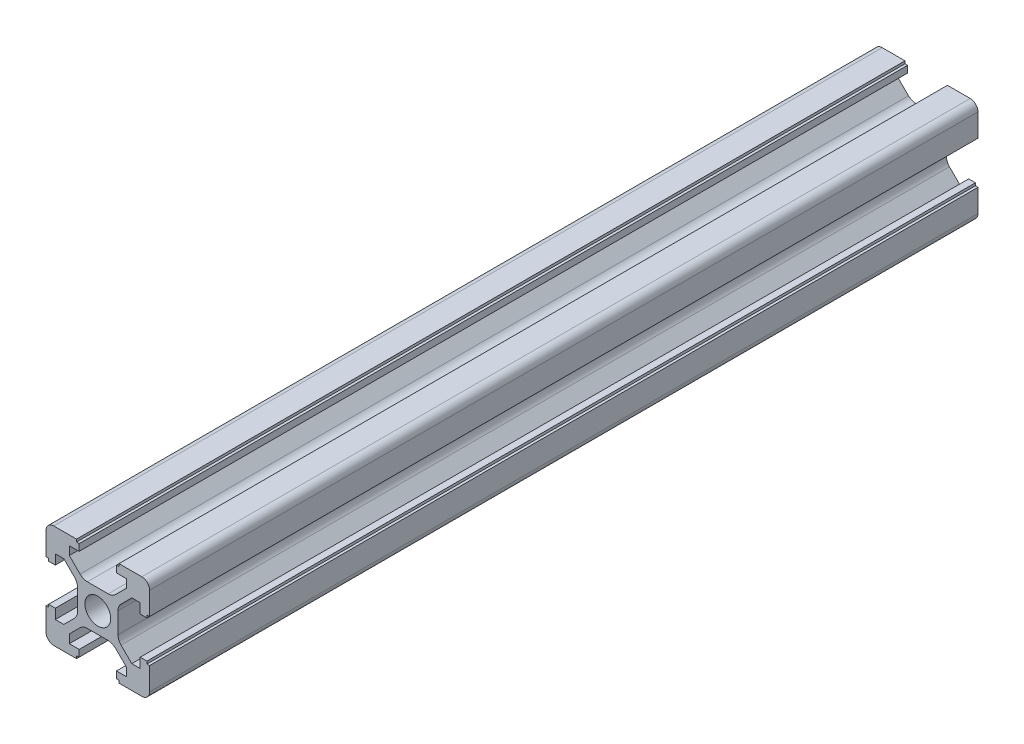
SolidWorks part; units mm, degrees
ref_plane "Front Plane" through (0, 0, 0) normal (0, 0, 1) x (1, 0, 0)
ref_plane "Top Plane" through (0, 0, 0) normal (0, 1, 0) x (1, 0, 0)
ref_plane "Right Plane" through (0, 0, 0) normal (1, 0, 0) x (0, 0, -1)
sketch "Sketch1" plane through (0, 0, 0) normal (0, 0, 1) x (1, 0, 0)
  line L0 (10, -4.1) -> (10, -8.5)
  line L1 (4.1, 10) -> (8.5, 10)
  line L2 (8.5, -10) -> (4.1, -10)
  line L3 (-8.5, -10) -> (-4.1, -10)
  line L4 (10, 8.5) -> (10, 4.1)
  line L7 (8.5, 10) -> (4.1, 10)
  line L8 (5.5, 6.5607) -> (3.4251, 4.4858)
  line L9 (8.5, 10) -> (4.1, 10)
  line L10 (3.9, 2.0109) -> (3.9, -2.0109)
  line L11 (2.0109, -3.9) -> (-2.0109, -3.9)
  line L12 (-3.9, -2.0109) -> (-3.9, 2.0109)
  line L13 (-2.0109, 3.9) -> (2.8393, 3.9)
  line L14 (2.5, 0) -> (22.2403, 0) construction
  line L15 (3.6, 9.5) -> (3.6, 8.2)
  line L16 (9.5, 3.6) -> (8.2, 3.6)
  line L17 (8.2, 3.6) -> (8.2, 5.5)
  line L18 (8.2, 5.5) -> (6.5607, 5.5)
  line L19 (10, -4.1) -> (10, -8.5)
  line L20 (4.1, 9.5) -> (3.6, 9.5)
  line L21 (4.1, 10) -> (4.1, 9.5)
  line L22 (8.5, 10) -> (4.1, 10)
  line L23 (10, 4.1) -> (9.5, 4.1)
  line L24 (9.5, 4.1) -> (9.5, 3.6)
  line L25 (5.5, 8.2) -> (5.5, 6.5607)
  line L26 (3.6, 8.2) -> (5.5, 8.2)
  line L27 (4.4858, 3.4251) -> (6.5607, 5.5)
  line L28 (10, -8.5) -> (10, -4.1)
  line L29 (6.5607, -5.5) -> (4.4858, -3.4251)
  line L30 (10, -8.5) -> (10, -4.1)
  line L31 (2.0109, -3.9) -> (-2.0109, -3.9)
  line L32 (3.9, 2.8393) -> (3.9, -2.0109)
  line L33 (9.5, -3.6) -> (8.2, -3.6)
  line L34 (3.6, -9.5) -> (3.6, -8.2)
  line L35 (3.6, -8.2) -> (5.5, -8.2)
  line L36 (5.5, -8.2) -> (5.5, -6.5607)
  line L37 (9.5, -4.1) -> (9.5, -3.6)
  line L38 (10, -4.1) -> (9.5, -4.1)
  line L39 (10, -8.5) -> (10, -4.1)
  line L40 (4.1, -10) -> (4.1, -9.5)
  line L41 (4.1, -9.5) -> (3.6, -9.5)
  line L42 (8.2, -5.5) -> (6.5607, -5.5)
  line L43 (8.2, -3.6) -> (8.2, -5.5)
  line L44 (3.4251, -4.4858) -> (5.5, -6.5607)
  line L45 (-4.1, -10) -> (-8.5, -10)
  line L46 (-10, -8.5) -> (-10, -4.1)
  line L47 (-8.5, -10) -> (-4.1, -10)
  line L48 (-5.5, -6.5607) -> (-3.4251, -4.4858)
  line L49 (-8.5, -10) -> (-4.1, -10)
  line L50 (-3.9, -2.0109) -> (-3.9, 2.0109)
  line L51 (2.0109, -3.9) -> (-2.0109, -3.9)
  line L52 (-3.6, -9.5) -> (-3.6, -8.2)
  line L53 (-9.5, -3.6) -> (-8.2, -3.6)
  line L54 (-8.2, -3.6) -> (-8.2, -5.5)
  line L55 (-8.2, -5.5) -> (-6.5607, -5.5)
  line L56 (-4.1, -9.5) -> (-3.6, -9.5)
  line L57 (-4.1, -10) -> (-4.1, -9.5)
  line L58 (-8.5, -10) -> (-4.1, -10)
  line L59 (-10, -4.1) -> (-9.5, -4.1)
  line L60 (-9.5, -4.1) -> (-9.5, -3.6)
  line L61 (-5.5, -8.2) -> (-5.5, -6.5607)
  line L62 (-3.6, -8.2) -> (-5.5, -8.2)
  line L63 (-4.4858, -3.4251) -> (-6.5607, -5.5)
  line L64 (-10, 4.1) -> (-10, 8.5)
  line L65 (-8.5, 10) -> (-4.1, 10)
  line L66 (-10, 8.5) -> (-10, 4.1)
  line L67 (-6.5607, 5.5) -> (-4.4858, 3.4251)
  line L68 (-10, 8.5) -> (-10, 4.1)
  line L69 (-2.0109, 3.9) -> (2.0109, 3.9)
  line L70 (-3.9, -2.0109) -> (-3.9, 2.0109)
  line L71 (-9.5, 3.6) -> (-8.2, 3.6)
  line L72 (-3.6, 9.5) -> (-3.6, 8.2)
  line L73 (-3.6, 8.2) -> (-5.5, 8.2)
  line L74 (-5.5, 8.2) -> (-5.5, 6.5607)
  line L75 (-9.5, 4.1) -> (-9.5, 3.6)
  line L76 (-10, 4.1) -> (-9.5, 4.1)
  line L77 (-10, 8.5) -> (-10, 4.1)
  line L78 (-4.1, 10) -> (-4.1, 9.5)
  line L79 (-4.1, 9.5) -> (-3.6, 9.5)
  line L80 (-8.2, 5.5) -> (-6.5607, 5.5)
  line L81 (-8.2, 3.6) -> (-8.2, 5.5)
  line L82 (-3.4251, 4.4858) -> (-5.5, 6.5607)
  line L83 (4.1, -10) -> (8.5, -10)
  arc A0 (2.0109, -3.9) -> (3.4251, -4.4858) centre (2.0109, -5.9) cw
  arc A1 (4.4858, -3.4251) -> (3.9, -2.0109) centre (5.9, -2.0109) cw
  arc A2 (3.9, 2.0109) -> (4.4858, 3.4251) centre (5.9, 2.0109) cw
  arc A3 (2.0109, 3.9) -> (3.4251, 4.4858) centre (2.0109, 5.9) ccw
  arc A4 (-2.0109, 3.9) -> (-3.4251, 4.4858) centre (-2.0109, 5.9) cw
  arc A5 (-4.4858, 3.4251) -> (-3.9, 2.0109) centre (-5.9, 2.0109) cw
  arc A6 (-3.4251, -4.4858) -> (-2.0109, -3.9) centre (-2.0109, -5.9) cw
  arc A7 (-3.9, -2.0109) -> (-4.4858, -3.4251) centre (-5.9, -2.0109) cw
  circle A8 centre (0, 0) radius 2.5
  arc A9 (-8.5, -10) -> (-10, -8.5) centre (-8.5, -8.5) cw
  arc A10 (-10, 8.5) -> (-8.5, 10) centre (-8.5, 8.5) cw
  arc A11 (8.5, 10) -> (10, 8.5) centre (8.5, 8.5) cw
  arc A12 (8.5, -10) -> (10, -8.5) centre (8.5, -8.5) ccw
  point P0 (0, 0)
  point P86 (0, 0)
  point P107 (10, -10)
  dimension "D3" = 2
  dimension "D5" = 5
  dimension "D2" = 1.5
  dimension "D8" = 1.5
  dimension "D4" = 6.1
  dimension "D6" = 4
  dimension "D11" = 0.5
  dimension "D12" = 0.5
extrude "Boss-Extrude2" add sketch "Sketch1" along normal blind 160
